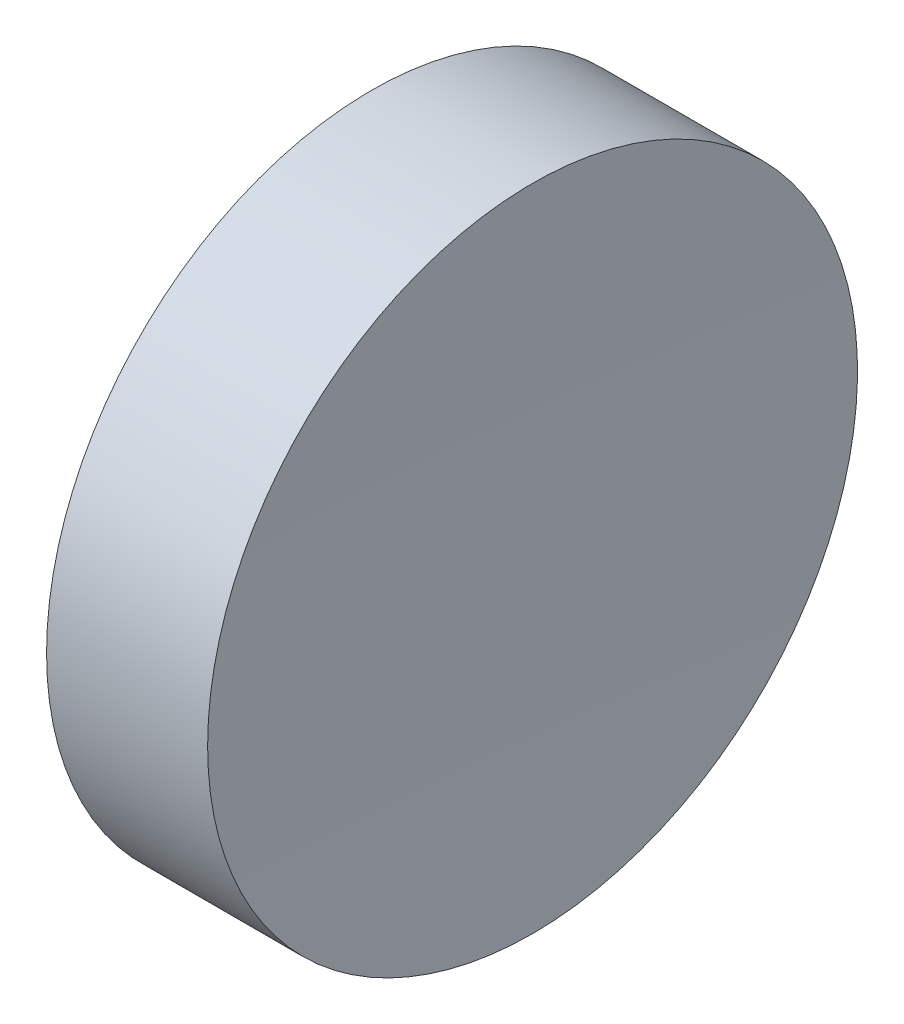
SolidWorks part; units mm, degrees
ref_plane "前视基准面" through (0, 0, 0) normal (0, 0, 1) x (1, 0, 0)
ref_plane "上视基准面" through (0, 0, 0) normal (0, 1, 0) x (1, 0, 0)
ref_plane "右视基准面" through (0, 0, 0) normal (1, 0, 0) x (0, 0, -1)
sketch "草图1" plane through (0, 0, 0) normal (0, 0, 1) x (1, 0, 0)
  line L0 (108.9851, 69.378) -> (132.7763, 69.378) construction
  line L1 (115.0927, 69.378) -> (115.0927, 81.878)
  line L2 (115.0927, 81.878) -> (121.288, 81.878)
  line L3 (121.0927, 69.378) -> (115.0927, 69.378)
  arc A0 (121.288, 81.878) -> (121.0927, 69.378) centre (521.0927, 69.378) ccw
revolve "旋转1" add sketch "草图1" angle 360 about L0
